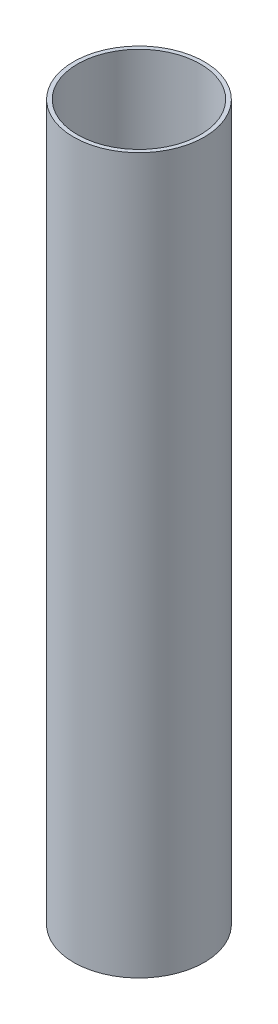
SolidWorks part; units mm, degrees
ref_plane "Front Plane" through (0, 0, 0) normal (0, 0, 1) x (1, 0, 0)
ref_plane "Top Plane" through (0, 0, 0) normal (0, 1, 0) x (1, 0, 0)
ref_plane "Right Plane" through (0, 0, 0) normal (1, 0, 0) x (0, 0, -1)
sketch "Sketch1" plane through (0, 0, 0) normal (0, 1, 0) x (1, 0, 0)
  circle A0 centre (0, 0) radius 27
  circle A1 centre (0, 0) radius 25.35
  dimension "D1" = 54
  dimension "D2" = 50.7
extrude "Boss-Extrude1" add sketch "Sketch1" along normal blind 295.275
